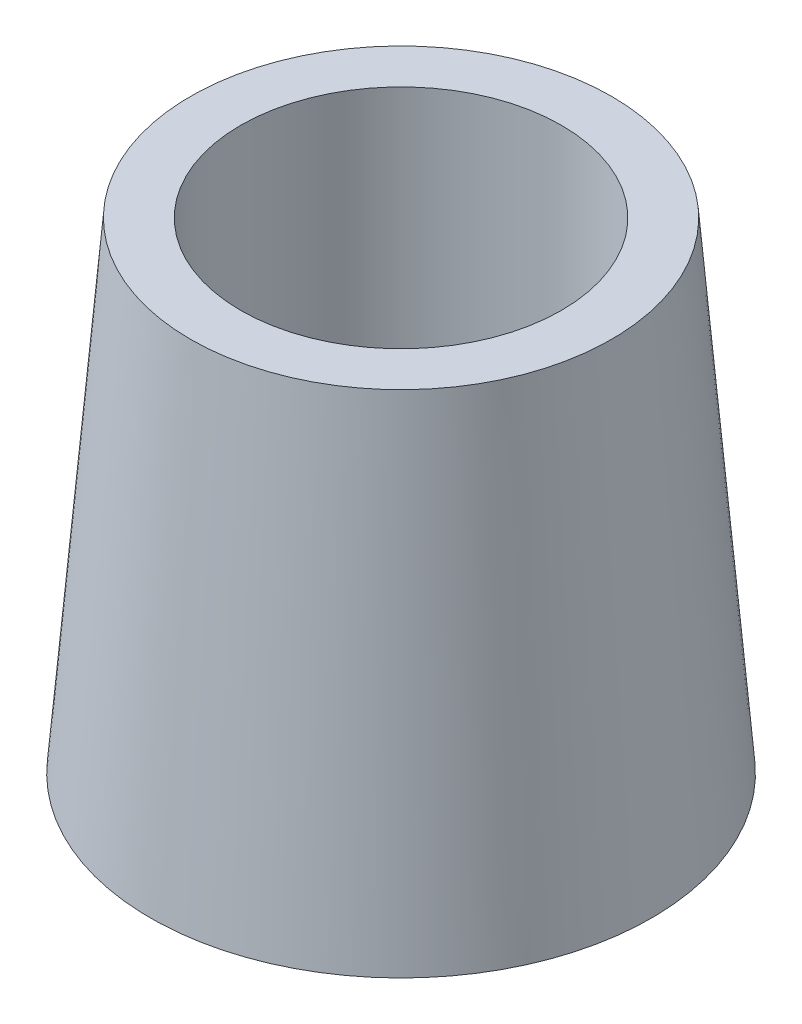
SolidWorks part; units mm, degrees
ref_plane "Front Plane" through (0, 0, 0) normal (0, 0, 1) x (1, 0, 0)
ref_plane "Top Plane" through (0, 0, 0) normal (0, 1, 0) x (1, 0, 0)
ref_plane "Right Plane" through (0, 0, 0) normal (1, 0, 0) x (0, 0, -1)
sketch "Sketch1" plane through (0, 0, 0) normal (0, 0, 1) x (1, 0, 0)
  line L0 (8, 0) -> (12.5, 0)
  line L1 (12.5, 0) -> (10.5, 24)
  line L2 (10.5, 24) -> (8, 24)
  line L4 (8, 24) -> (8, 0)
  line L5 (0, 0) -> (0, 5.9834) construction
  dimension "D1" = 12.5
  dimension "D2" = 8
  dimension "D3" = 24
  dimension "D4" = 10.5
revolve "Revolve1" add sketch "Sketch1" angle 360 about L5
